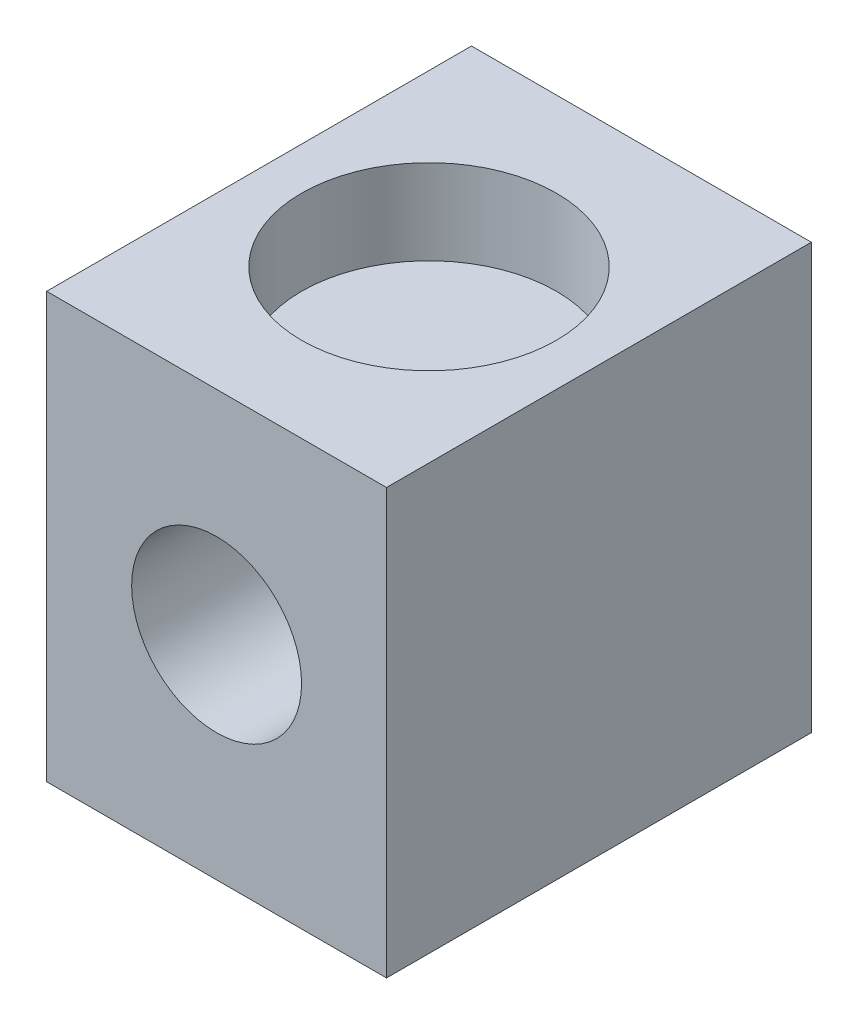
SolidWorks part; units mm, degrees
ref_plane "Alzado" through (0, 0, 0) normal (0, 0, 1) x (1, 0, 0)
ref_plane "Planta" through (0, 0, 0) normal (0, 1, 0) x (1, 0, 0)
ref_plane "Vista lateral" through (0, 0, 0) normal (1, 0, 0) x (0, 0, -1)
sketch "Croquis1" plane through (0, 0, 0) normal (0, 0, 1) x (1, 0, 0)
  line L1 (-2, -2.5) -> (2, -2.5)
  line L2 (-2, -2.5) -> (-2, 2.5)
  line L3 (-2, 2.5) -> (2, 2.5)
  line L4 (2, -2.5) -> (2, 2.5)
  line L5 (-2, -2.5) -> (2, 2.5) construction
  line L6 (-2, 2.5) -> (2, -2.5) construction
  circle A0 centre (0, 0) radius 1
  point P0 (0, 0)
  dimension "D3" = 2
  dimension "D1" = 4
  dimension "D2" = 5
extrude "Saliente-Extruir1" add sketch "Croquis1" along normal blind 5
sketch "Croquis3" plane through (0, 2.5, 0) normal (0, 1, 0) x (1, 0, 0)
  circle A0 centre (0, -2.5) radius 1.5
  dimension "D1" = 3
extrude "Cortar-Extruir1" cut sketch "Croquis3" against normal blind 1 contours A0
ref_plane "Plano1" through (0, 0, 0) normal (0, -1, 0) x (-1, 0, 0)
mirror "Simetría1" about plane through (0, 0, 0) normal (0, -1, 0) of "Cortar-Extruir1"
